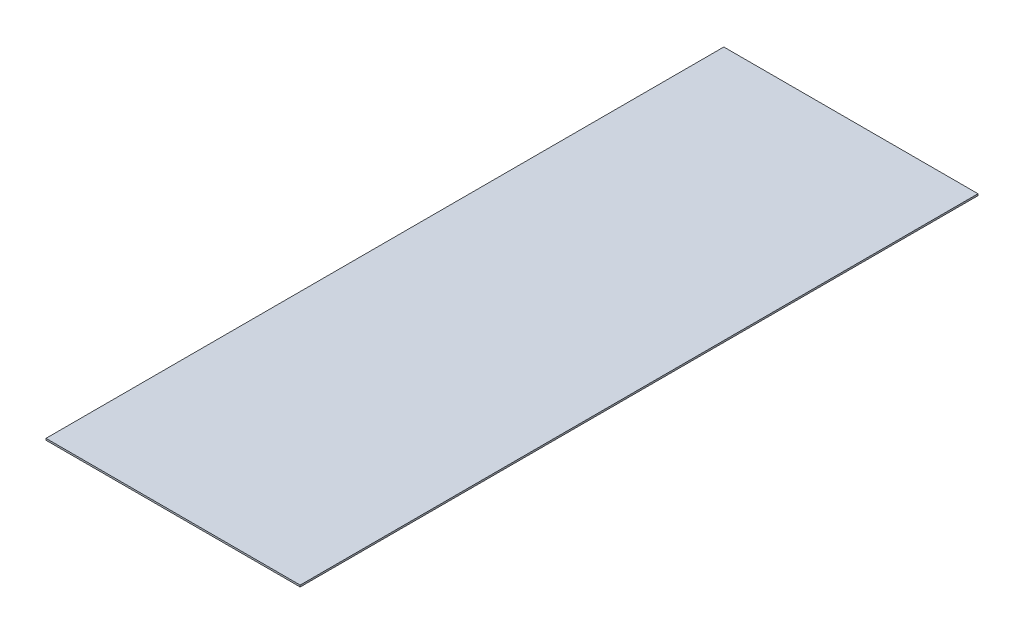
SolidWorks part; units mm, degrees
material "Pure Silver"
ref_plane "Front Plane" through (0, 0, 0) normal (0, 0, 1) x (1, 0, 0)
ref_plane "Top Plane" through (0, 0, 0) normal (0, 1, 0) x (1, 0, 0)
ref_plane "Right Plane" through (0, 0, 0) normal (1, 0, 0) x (0, 0, -1)
sketch "Sketch1" plane through (0, 0, 0) normal (0, 1, 0) x (1, 0, 0)
  line L1 (-0.75, 2) -> (0.75, 2)
  line L2 (-0.75, 2) -> (-0.75, -2)
  line L3 (-0.75, -2) -> (0.75, -2)
  line L4 (0.75, 2) -> (0.75, -2)
  line L5 (-0.75, 2) -> (0.75, -2) construction
  line L6 (-0.75, -2) -> (0.75, 2) construction
  point P0 (0, 0)
  dimension "D1" = 1.5
  dimension "D2" = 4
extrude "Boss-Extrude1" add sketch "Sketch1" along normal blind 0.01
